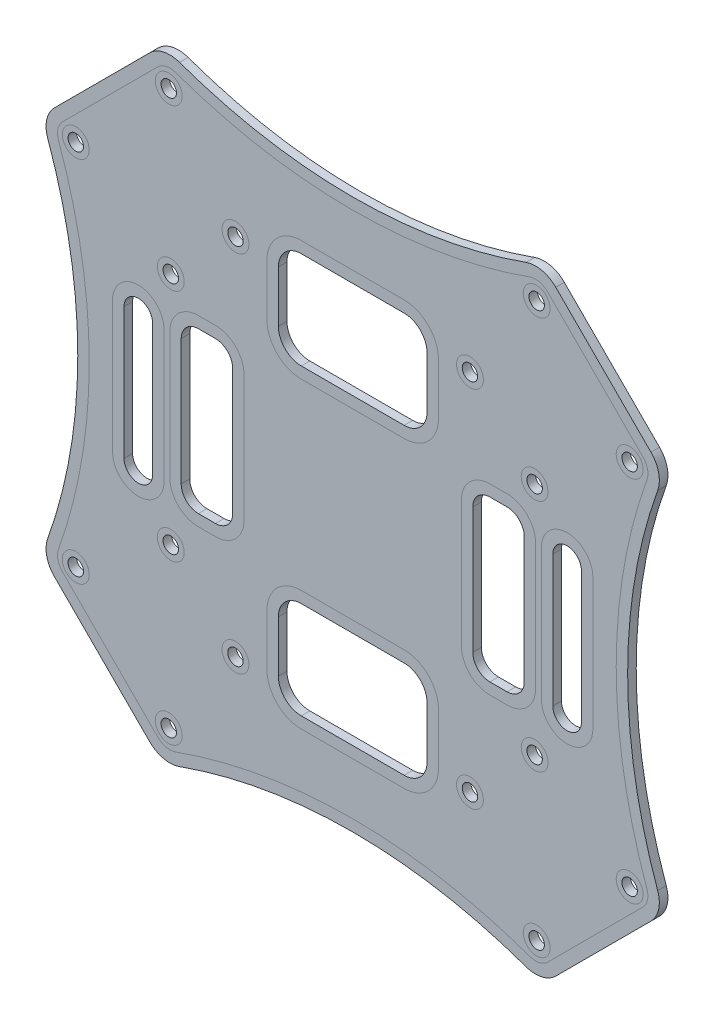
SolidWorks part; units mm, degrees
ref_plane "Ön Düzlem" through (0, 0, 0) normal (0, 0, 1) x (1, 0, 0)
ref_plane "Üst Düzlem" through (0, 0, 0) normal (0, 1, 0) x (1, 0, 0)
ref_plane "Sağ Düzlem" through (0, 0, 0) normal (1, 0, 0) x (0, 0, -1)
sketch "Çizim1" plane through (0, 0, 0) normal (0, 0, 1) x (1, 0, 0)
  line L2 (43.8406, -43.8406) -> (54.4472, -33.234)
  line L3 (43.8406, 43.8406) -> (54.4472, 33.234)
  line L4 (-9, 18) -> (9, 18)
  line L5 (-13, 22) -> (-13, 31)
  line L6 (-43.8406, 43.8406) -> (-54.4472, 33.234)
  line L7 (-43.8406, -43.8406) -> (-54.4472, -33.234)
  line L8 (-9, 35) -> (9, 35)
  line L9 (-43.8406, 43.8406) -> (-33.234, 54.4472)
  line L10 (43.8406, 43.8406) -> (33.234, 54.4472)
  line L11 (-43.8406, -43.8406) -> (-33.234, -54.4472)
  line L12 (43.8406, -43.8406) -> (33.234, -54.4472)
  line L13 (13, 22) -> (13, 31)
  line L17 (13, -22) -> (13, -31)
  line L18 (-9, -35) -> (9, -35)
  line L19 (-13, -22) -> (-13, -31)
  line L20 (-9, -18) -> (9, -18)
  line L21 (37.5, -11.5) -> (37.5, 11.5) construction
  line L22 (35, -11.5) -> (35, 11.5)
  line L23 (40, -11.5) -> (40, 11.5)
  line L24 (-37.5, -11.5) -> (-37.5, 11.5) construction
  line L25 (24, -13.3629) -> (27, -13.3629)
  line L26 (21, -10.3629) -> (21, 11.6371)
  line L27 (24, 14.6371) -> (27, 14.6371)
  line L28 (30, -10.3629) -> (30, 11.6371)
  line L31 (-35, -11.5) -> (-35, 11.5)
  line L32 (-40, -11.5) -> (-40, 11.5)
  line L35 (-30, -10.3629) -> (-30, 11.6371)
  line L36 (-24, 14.6371) -> (-27, 14.6371)
  line L37 (-21, -10.3629) -> (-21, 11.6371)
  line L38 (-24, -13.3629) -> (-27, -13.3629)
  arc A0 (54.4472, 33.234) -> (54.4472, -33.234) centre (138.0863, 0) ccw
  arc A1 (-54.4472, 33.234) -> (-54.4472, -33.234) centre (-138.0863, 0) cw
  arc A2 (-33.234, 54.4472) -> (33.234, 54.4472) centre (0, 138.0863) ccw
  arc A3 (-33.234, -54.4472) -> (33.234, -54.4472) centre (0, -138.0863) cw
  arc A4 (-13, 31) -> (-9, 35) centre (-9, 31) cw
  arc A5 (-9, 18) -> (-13, 22) centre (-9, 22) cw
  arc A6 (9, 18) -> (13, 22) centre (9, 22) ccw
  arc A7 (9, 35) -> (13, 31) centre (9, 31) cw
  arc A8 (9, -35) -> (13, -31) centre (9, -31) ccw
  arc A9 (9, -18) -> (13, -22) centre (9, -22) cw
  arc A10 (-9, -18) -> (-13, -22) centre (-9, -22) ccw
  arc A11 (-13, -31) -> (-9, -35) centre (-9, -31) ccw
  arc A12 (35, -11.5) -> (40, -11.5) centre (37.5, -11.5) ccw
  arc A13 (40, 11.5) -> (35, 11.5) centre (37.5, 11.5) ccw
  arc A14 (27, 14.6371) -> (30, 11.6371) centre (27, 11.6371) cw
  arc A15 (21, 11.6371) -> (24, 14.6371) centre (24, 11.6371) cw
  arc A16 (24, -13.3629) -> (21, -10.3629) centre (24, -10.3629) cw
  arc A17 (27, -13.3629) -> (30, -10.3629) centre (27, -10.3629) ccw
  arc A18 (-35, -11.5) -> (-40, -11.5) centre (-37.5, -11.5) cw
  arc A19 (-40, 11.5) -> (-35, 11.5) centre (-37.5, 11.5) cw
  arc A20 (-27, -13.3629) -> (-30, -10.3629) centre (-27, -10.3629) cw
  arc A21 (-24, -13.3629) -> (-21, -10.3629) centre (-24, -10.3629) ccw
  arc A22 (-21, 11.6371) -> (-24, 14.6371) centre (-24, 11.6371) ccw
  arc A23 (-27, 14.6371) -> (-30, 11.6371) centre (-27, 11.6371) ccw
  circle A24 centre (-32.1734, 48.4368) radius 1.35
  circle A25 centre (-48.4368, 32.1734) radius 1.35
  circle A26 centre (-31.8198, 20.5061) radius 1.35
  circle A27 centre (-20.5061, 31.8198) radius 1.35
  circle A28 centre (48.4368, 32.1734) radius 1.35
  circle A29 centre (32.1734, 48.4368) radius 1.35
  circle A30 centre (31.8198, 20.5061) radius 1.35
  circle A31 centre (20.5061, 31.8198) radius 1.35
  circle A32 centre (32.1734, -48.4368) radius 1.35
  circle A33 centre (48.4368, -32.1734) radius 1.35
  circle A34 centre (31.8198, -20.5061) radius 1.35
  circle A35 centre (20.5061, -31.8198) radius 1.35
  circle A36 centre (-32.1734, -48.4368) radius 1.35
  circle A37 centre (-48.4368, -32.1734) radius 1.35
  circle A38 centre (-31.8198, -20.5061) radius 1.35
  circle A39 centre (-20.5061, -31.8198) radius 1.35
  point P54 (37.5, 0)
  point P79 (-37.5, 0)
  dimension "D1" = 4
  dimension "D2" = 3
extrude "Yükseklik-Ekstrüzyon1" add sketch "Çizim1" along normal blind 1.5
fillet "Radyus1" radius 5 8 edges at (33.234, 54.4472, 0.75) (54.4472, 33.234, 0.75) (54.4472, -33.234, 0.75) (33.234, -54.4472, 0.75) (-33.234, -54.4472, 0.75) (-54.4472, -33.234, 0.75) (-54.4472, 33.234, 0.75) (-33.234, 54.4472, 0.75)
sketch "Çizim2" plane through (0, 0, 1.5) normal (0, 0, 1) x (1, 0, 0)
  line L8 (50.752, 34.1008) -> (34.1008, 50.752)
  line L9 (-34.1008, 50.752) -> (-50.752, 34.1008)
  line L10 (-50.752, -34.1008) -> (-34.1008, -50.752)
  line L11 (34.1008, -50.752) -> (50.752, -34.1008)
  line L12 (50.752, 34.1008) -> (34.1008, 50.752)
  line L13 (-34.1008, 50.752) -> (-50.752, 34.1008)
  line L14 (-50.752, -34.1008) -> (-34.1008, -50.752)
  line L15 (34.1008, -50.752) -> (50.752, -34.1008)
  line L48 (15, 22) -> (15, 31)
  line L49 (-9, 16) -> (9, 16)
  line L50 (15, 22) -> (15, 31)
  line L51 (-9, 16) -> (9, 16)
  line L57 (-15, 31) -> (-15, 22)
  line L58 (9, 37) -> (-9, 37)
  line L59 (-15, 31) -> (-15, 22)
  line L60 (9, 37) -> (-9, 37)
  line L83 (15, -31) -> (15, -22)
  line L84 (-9, -37) -> (9, -37)
  line L85 (-15, -22) -> (-15, -31)
  line L86 (9, -16) -> (-9, -16)
  line L87 (15, -31) -> (15, -22)
  line L88 (-9, -37) -> (9, -37)
  line L89 (-15, -22) -> (-15, -31)
  line L90 (9, -16) -> (-9, -16)
  line L111 (24, -15.3629) -> (27, -15.3629)
  line L112 (19, 11.6371) -> (19, -10.3629)
  line L113 (27, 16.6371) -> (24, 16.6371)
  line L114 (32, -10.3629) -> (32, 11.6371)
  line L115 (24, -15.3629) -> (27, -15.3629)
  line L116 (19, 11.6371) -> (19, -10.3629)
  line L117 (27, 16.6371) -> (24, 16.6371)
  line L118 (32, -10.3629) -> (32, 11.6371)
  line L124 (42, -11.5) -> (42, 11.5)
  line L125 (33, 11.5) -> (33, -11.5)
  line L126 (42, -11.5) -> (42, 11.5)
  line L127 (33, 11.5) -> (33, -11.5)
  line L151 (-24, 16.6371) -> (-27, 16.6371)
  line L152 (-32, 11.6371) -> (-32, -10.3629)
  line L153 (-27, -15.3629) -> (-24, -15.3629)
  line L154 (-19, -10.3629) -> (-19, 11.6371)
  line L155 (-24, 16.6371) -> (-27, 16.6371)
  line L156 (-32, 11.6371) -> (-32, -10.3629)
  line L157 (-27, -15.3629) -> (-24, -15.3629)
  line L158 (-19, -10.3629) -> (-19, 11.6371)
  line L162 (-42, 11.5) -> (-42, -11.5)
  line L163 (-33, -11.5) -> (-33, 11.5)
  line L164 (-42, 11.5) -> (-42, -11.5)
  line L165 (-33, -11.5) -> (-33, 11.5)
  arc A24 (34.1008, 50.752) -> (30.9696, 51.4556) centre (31.9795, 48.6307) ccw
  arc A25 (-30.9696, 51.4556) -> (30.9696, 51.4556) centre (0, 138.0863) ccw
  arc A26 (-30.9696, 51.4556) -> (-34.1008, 50.752) centre (-31.9795, 48.6307) ccw
  arc A27 (-50.752, 34.1008) -> (-51.4556, 30.9696) centre (-48.6307, 31.9795) ccw
  arc A28 (-51.4556, -30.9696) -> (-51.4556, 30.9696) centre (-138.0863, 0) ccw
  arc A29 (-51.4556, -30.9696) -> (-50.752, -34.1008) centre (-48.6307, -31.9795) ccw
  arc A30 (-34.1008, -50.752) -> (-30.9696, -51.4556) centre (-31.9795, -48.6307) ccw
  arc A31 (30.9696, -51.4556) -> (-30.9696, -51.4556) centre (0, -138.0863) ccw
  arc A32 (30.9696, -51.4556) -> (34.1008, -50.752) centre (31.9795, -48.6307) ccw
  arc A33 (50.752, -34.1008) -> (51.4556, -30.9696) centre (48.6307, -31.9795) ccw
  arc A34 (51.4556, 30.9696) -> (51.4556, -30.9696) centre (138.0863, 0) ccw
  arc A35 (51.4556, 30.9696) -> (50.752, 34.1008) centre (48.6307, 31.9795) ccw
  arc A36 (34.1008, 50.752) -> (30.9696, 51.4556) centre (31.9795, 48.6307) ccw
  arc A37 (-30.9696, 51.4556) -> (30.9696, 51.4556) centre (0, 138.0863) ccw
  arc A38 (-30.9696, 51.4556) -> (-34.1008, 50.752) centre (-31.9795, 48.6307) ccw
  arc A39 (-50.752, 34.1008) -> (-51.4556, 30.9696) centre (-48.6307, 31.9795) ccw
  arc A40 (-51.4556, -30.9696) -> (-51.4556, 30.9696) centre (-138.0863, 0) ccw
  arc A41 (-51.4556, -30.9696) -> (-50.752, -34.1008) centre (-48.6307, -31.9795) ccw
  arc A42 (-34.1008, -50.752) -> (-30.9696, -51.4556) centre (-31.9795, -48.6307) ccw
  arc A43 (30.9696, -51.4556) -> (-30.9696, -51.4556) centre (0, -138.0863) ccw
  arc A44 (30.9696, -51.4556) -> (34.1008, -50.752) centre (31.9795, -48.6307) ccw
  arc A45 (50.752, -34.1008) -> (51.4556, -30.9696) centre (48.6307, -31.9795) ccw
  arc A46 (51.4556, 30.9696) -> (51.4556, -30.9696) centre (138.0863, 0) ccw
  arc A47 (51.4556, 30.9696) -> (50.752, 34.1008) centre (48.6307, 31.9795) ccw
  arc A107 (15, 31) -> (9, 37) centre (9, 31) ccw
  arc A108 (9, 16) -> (15, 22) centre (9, 22) ccw
  arc A109 (-15, 22) -> (-9, 16) centre (-9, 22) ccw
  arc A110 (15, 31) -> (9, 37) centre (9, 31) ccw
  arc A111 (9, 16) -> (15, 22) centre (9, 22) ccw
  arc A112 (-15, 22) -> (-9, 16) centre (-9, 22) ccw
  arc A113 (-9, 37) -> (-15, 31) centre (-9, 31) ccw
  arc A114 (-9, 37) -> (-15, 31) centre (-9, 31) ccw
  circle A129 centre (-32.1734, 48.4368) radius 2.35
  circle A130 centre (-32.1734, 48.4368) radius 2.35
  circle A132 centre (-20.5061, 31.8198) radius 2.35
  circle A133 centre (-20.5061, 31.8198) radius 2.35
  circle A135 centre (-31.8198, 20.5061) radius 2.35
  circle A136 centre (-31.8198, 20.5061) radius 2.35
  circle A138 centre (-48.4368, 32.1734) radius 2.35
  circle A139 centre (-48.4368, 32.1734) radius 2.35
  circle A141 centre (32.1734, 48.4368) radius 2.35
  circle A142 centre (32.1734, 48.4368) radius 2.35
  circle A144 centre (20.5061, 31.8198) radius 2.35
  circle A145 centre (20.5061, 31.8198) radius 2.35
  circle A147 centre (31.8198, 20.5061) radius 2.35
  circle A148 centre (31.8198, 20.5061) radius 2.35
  circle A150 centre (48.4368, 32.1734) radius 2.35
  circle A151 centre (48.4368, 32.1734) radius 2.35
  circle A153 centre (31.8198, -20.5061) radius 2.35
  circle A154 centre (31.8198, -20.5061) radius 2.35
  circle A156 centre (48.4368, -32.1734) radius 2.35
  circle A157 centre (48.4368, -32.1734) radius 2.35
  circle A159 centre (20.5061, -31.8198) radius 2.35
  circle A160 centre (20.5061, -31.8198) radius 2.35
  circle A162 centre (32.1734, -48.4368) radius 2.35
  circle A163 centre (32.1734, -48.4368) radius 2.35
  circle A165 centre (-20.5061, -31.8198) radius 2.35
  circle A166 centre (-20.5061, -31.8198) radius 2.35
  circle A168 centre (-31.8198, -20.5061) radius 2.35
  circle A169 centre (-31.8198, -20.5061) radius 2.35
  circle A171 centre (-48.4368, -32.1734) radius 2.35
  circle A172 centre (-48.4368, -32.1734) radius 2.35
  circle A174 centre (-32.1734, -48.4368) radius 2.35
  circle A175 centre (-32.1734, -48.4368) radius 2.35
  arc A195 (15, -22) -> (9, -16) centre (9, -22) ccw
  arc A196 (9, -37) -> (15, -31) centre (9, -31) ccw
  arc A197 (-15, -31) -> (-9, -37) centre (-9, -31) ccw
  arc A198 (-9, -16) -> (-15, -22) centre (-9, -22) ccw
  arc A199 (15, -22) -> (9, -16) centre (9, -22) ccw
  arc A200 (9, -37) -> (15, -31) centre (9, -31) ccw
  arc A201 (-15, -31) -> (-9, -37) centre (-9, -31) ccw
  arc A202 (-9, -16) -> (-15, -22) centre (-9, -22) ccw
  arc A219 (27, -15.3629) -> (32, -10.3629) centre (27, -10.3629) ccw
  arc A220 (19, -10.3629) -> (24, -15.3629) centre (24, -10.3629) ccw
  arc A221 (24, 16.6371) -> (19, 11.6371) centre (24, 11.6371) ccw
  arc A222 (32, 11.6371) -> (27, 16.6371) centre (27, 11.6371) ccw
  arc A223 (27, -15.3629) -> (32, -10.3629) centre (27, -10.3629) ccw
  arc A224 (19, -10.3629) -> (24, -15.3629) centre (24, -10.3629) ccw
  arc A225 (24, 16.6371) -> (19, 11.6371) centre (24, 11.6371) ccw
  arc A226 (32, 11.6371) -> (27, 16.6371) centre (27, 11.6371) ccw
  arc A229 (33, -11.5) -> (42, -11.5) centre (37.5, -11.5) ccw
  arc A230 (42, 11.5) -> (33, 11.5) centre (37.5, 11.5) ccw
  arc A231 (33, -11.5) -> (42, -11.5) centre (37.5, -11.5) ccw
  arc A232 (42, 11.5) -> (33, 11.5) centre (37.5, 11.5) ccw
  arc A251 (-19, 11.6371) -> (-24, 16.6371) centre (-24, 11.6371) ccw
  arc A252 (-27, 16.6371) -> (-32, 11.6371) centre (-27, 11.6371) ccw
  arc A253 (-32, -10.3629) -> (-27, -15.3629) centre (-27, -10.3629) ccw
  arc A254 (-24, -15.3629) -> (-19, -10.3629) centre (-24, -10.3629) ccw
  arc A255 (-19, 11.6371) -> (-24, 16.6371) centre (-24, 11.6371) ccw
  arc A256 (-27, 16.6371) -> (-32, 11.6371) centre (-27, 11.6371) ccw
  arc A257 (-32, -10.3629) -> (-27, -15.3629) centre (-27, -10.3629) ccw
  arc A258 (-24, -15.3629) -> (-19, -10.3629) centre (-24, -10.3629) ccw
  arc A262 (-42, -11.5) -> (-33, -11.5) centre (-37.5, -11.5) ccw
  arc A263 (-33, 11.5) -> (-42, 11.5) centre (-37.5, 11.5) ccw
  arc A264 (-42, -11.5) -> (-33, -11.5) centre (-37.5, -11.5) ccw
  arc A265 (-33, 11.5) -> (-42, 11.5) centre (-37.5, 11.5) ccw
  dimension "D1" = 2
  dimension "D2" = 2
  dimension "D3" = 2
  dimension "D4" = 1
  dimension "D5" = 1
  dimension "D6" = 1
  dimension "D7" = 1
  dimension "D8" = 1
  dimension "D9" = 1
  dimension "D10" = 1
  dimension "D11" = 1
  dimension "D12" = 1
  dimension "D13" = 1
  dimension "D14" = 1
  dimension "D15" = 1
  dimension "D16" = 1
  dimension "D17" = 1
  dimension "D18" = 1
  dimension "D19" = 1
  dimension "D20" = 2
  dimension "D21" = 2
  dimension "D22" = 2
  dimension "D23" = 2
  dimension "D24" = 2
split line "Ayrım Çizgisi1"
sketch "Çizim3" plane through (0, 0, 0) normal (0, 0, -1) x (-1, 0, 0)
  line L8 (-34.1008, 50.752) -> (-50.752, 34.1008)
  line L9 (-50.752, -34.1008) -> (-34.1008, -50.752)
  line L10 (34.1008, -50.752) -> (50.752, -34.1008)
  line L11 (50.752, 34.1008) -> (34.1008, 50.752)
  line L12 (-34.1008, 50.752) -> (-50.752, 34.1008)
  line L13 (-50.752, -34.1008) -> (-34.1008, -50.752)
  line L14 (34.1008, -50.752) -> (50.752, -34.1008)
  line L15 (50.752, 34.1008) -> (34.1008, 50.752)
  line L36 (15, 22) -> (15, 31)
  line L37 (-9, 16) -> (9, 16)
  line L38 (-15, 31) -> (-15, 22)
  line L39 (9, 37) -> (-9, 37)
  line L40 (15, 22) -> (15, 31)
  line L41 (-9, 16) -> (9, 16)
  line L42 (-15, 31) -> (-15, 22)
  line L43 (9, 37) -> (-9, 37)
  line L76 (32, -10.3629) -> (32, 11.6371)
  line L77 (24, -15.3629) -> (27, -15.3629)
  line L78 (19, 11.6371) -> (19, -10.3629)
  line L79 (27, 16.6371) -> (24, 16.6371)
  line L80 (32, -10.3629) -> (32, 11.6371)
  line L81 (24, -15.3629) -> (27, -15.3629)
  line L82 (19, 11.6371) -> (19, -10.3629)
  line L83 (27, 16.6371) -> (24, 16.6371)
  line L88 (33, -11.5) -> (33, 11.5)
  line L89 (33, -11.5) -> (33, 11.5)
  line L94 (42, -11.5) -> (42, 11.5)
  line L95 (42, -11.5) -> (42, 11.5)
  line L119 (-27, -15.3629) -> (-24, -15.3629)
  line L120 (-32, 11.6371) -> (-32, -10.3629)
  line L121 (-24, 16.6371) -> (-27, 16.6371)
  line L122 (-19, -10.3629) -> (-19, 11.6371)
  line L123 (-27, -15.3629) -> (-24, -15.3629)
  line L124 (-32, 11.6371) -> (-32, -10.3629)
  line L125 (-24, 16.6371) -> (-27, 16.6371)
  line L126 (-19, -10.3629) -> (-19, 11.6371)
  line L130 (-42, 11.5) -> (-42, -11.5)
  line L131 (-33, -11.5) -> (-33, 11.5)
  line L132 (-42, 11.5) -> (-42, -11.5)
  line L133 (-33, -11.5) -> (-33, 11.5)
  line L156 (15, -31) -> (15, -22)
  line L157 (-9, -37) -> (9, -37)
  line L158 (-15, -22) -> (-15, -31)
  line L159 (9, -16) -> (-9, -16)
  line L160 (15, -31) -> (15, -22)
  line L161 (-9, -37) -> (9, -37)
  line L162 (-15, -22) -> (-15, -31)
  line L163 (9, -16) -> (-9, -16)
  arc A24 (-30.9696, 51.4556) -> (30.9696, 51.4556) centre (0, 138.0863) ccw
  arc A25 (-30.9696, 51.4556) -> (-34.1008, 50.752) centre (-31.9795, 48.6307) ccw
  arc A26 (-50.752, 34.1008) -> (-51.4556, 30.9696) centre (-48.6307, 31.9795) ccw
  arc A27 (-51.4556, -30.9696) -> (-51.4556, 30.9696) centre (-138.0863, 0) ccw
  arc A28 (-51.4556, -30.9696) -> (-50.752, -34.1008) centre (-48.6307, -31.9795) ccw
  arc A29 (-34.1008, -50.752) -> (-30.9696, -51.4556) centre (-31.9795, -48.6307) ccw
  arc A30 (30.9696, -51.4556) -> (-30.9696, -51.4556) centre (0, -138.0863) ccw
  arc A31 (30.9696, -51.4556) -> (34.1008, -50.752) centre (31.9795, -48.6307) ccw
  arc A32 (50.752, -34.1008) -> (51.4556, -30.9696) centre (48.6307, -31.9795) ccw
  arc A33 (51.4556, 30.9696) -> (51.4556, -30.9696) centre (138.0863, 0) ccw
  arc A34 (51.4556, 30.9696) -> (50.752, 34.1008) centre (48.6307, 31.9795) ccw
  arc A35 (34.1008, 50.752) -> (30.9696, 51.4556) centre (31.9795, 48.6307) ccw
  arc A36 (-30.9696, 51.4556) -> (30.9696, 51.4556) centre (0, 138.0863) ccw
  arc A37 (-30.9696, 51.4556) -> (-34.1008, 50.752) centre (-31.9795, 48.6307) ccw
  arc A38 (-50.752, 34.1008) -> (-51.4556, 30.9696) centre (-48.6307, 31.9795) ccw
  arc A39 (-51.4556, -30.9696) -> (-51.4556, 30.9696) centre (-138.0863, 0) ccw
  arc A40 (-51.4556, -30.9696) -> (-50.752, -34.1008) centre (-48.6307, -31.9795) ccw
  arc A41 (-34.1008, -50.752) -> (-30.9696, -51.4556) centre (-31.9795, -48.6307) ccw
  arc A42 (30.9696, -51.4556) -> (-30.9696, -51.4556) centre (0, -138.0863) ccw
  arc A43 (30.9696, -51.4556) -> (34.1008, -50.752) centre (31.9795, -48.6307) ccw
  arc A44 (50.752, -34.1008) -> (51.4556, -30.9696) centre (48.6307, -31.9795) ccw
  arc A45 (51.4556, 30.9696) -> (51.4556, -30.9696) centre (138.0863, 0) ccw
  arc A46 (51.4556, 30.9696) -> (50.752, 34.1008) centre (48.6307, 31.9795) ccw
  arc A47 (34.1008, 50.752) -> (30.9696, 51.4556) centre (31.9795, 48.6307) ccw
  arc A56 (15, 31) -> (9, 37) centre (9, 31) ccw
  arc A57 (9, 16) -> (15, 22) centre (9, 22) ccw
  arc A58 (-15, 22) -> (-9, 16) centre (-9, 22) ccw
  arc A59 (-9, 37) -> (-15, 31) centre (-9, 31) ccw
  arc A60 (15, 31) -> (9, 37) centre (9, 31) ccw
  arc A61 (9, 16) -> (15, 22) centre (9, 22) ccw
  arc A62 (-15, 22) -> (-9, 16) centre (-9, 22) ccw
  arc A63 (-9, 37) -> (-15, 31) centre (-9, 31) ccw
  arc A96 (27, -15.3629) -> (32, -10.3629) centre (27, -10.3629) ccw
  arc A97 (19, -10.3629) -> (24, -15.3629) centre (24, -10.3629) ccw
  arc A98 (24, 16.6371) -> (19, 11.6371) centre (24, 11.6371) ccw
  arc A99 (32, 11.6371) -> (27, 16.6371) centre (27, 11.6371) ccw
  arc A100 (27, -15.3629) -> (32, -10.3629) centre (27, -10.3629) ccw
  arc A101 (19, -10.3629) -> (24, -15.3629) centre (24, -10.3629) ccw
  arc A102 (24, 16.6371) -> (19, 11.6371) centre (24, 11.6371) ccw
  arc A103 (32, 11.6371) -> (27, 16.6371) centre (27, 11.6371) ccw
  arc A105 (42, 11.5) -> (33, 11.5) centre (37.5, 11.5) ccw
  arc A106 (33, -11.5) -> (42, -11.5) centre (37.5, -11.5) ccw
  arc A107 (42, 11.5) -> (33, 11.5) centre (37.5, 11.5) ccw
  arc A108 (33, -11.5) -> (42, -11.5) centre (37.5, -11.5) ccw
  arc A127 (-24, -15.3629) -> (-19, -10.3629) centre (-24, -10.3629) ccw
  arc A128 (-32, -10.3629) -> (-27, -15.3629) centre (-27, -10.3629) ccw
  arc A129 (-27, 16.6371) -> (-32, 11.6371) centre (-27, 11.6371) ccw
  arc A130 (-19, 11.6371) -> (-24, 16.6371) centre (-24, 11.6371) ccw
  arc A131 (-24, -15.3629) -> (-19, -10.3629) centre (-24, -10.3629) ccw
  arc A132 (-32, -10.3629) -> (-27, -15.3629) centre (-27, -10.3629) ccw
  arc A133 (-27, 16.6371) -> (-32, 11.6371) centre (-27, 11.6371) ccw
  arc A134 (-19, 11.6371) -> (-24, 16.6371) centre (-24, 11.6371) ccw
  arc A138 (-42, -11.5) -> (-33, -11.5) centre (-37.5, -11.5) ccw
  arc A139 (-33, 11.5) -> (-42, 11.5) centre (-37.5, 11.5) ccw
  arc A140 (-42, -11.5) -> (-33, -11.5) centre (-37.5, -11.5) ccw
  arc A141 (-33, 11.5) -> (-42, 11.5) centre (-37.5, 11.5) ccw
  circle A158 centre (-48.4368, 32.1734) radius 2.35
  circle A159 centre (-48.4368, 32.1734) radius 2.35
  arc A160 (15, -22) -> (9, -16) centre (9, -22) ccw
  arc A161 (9, -37) -> (15, -31) centre (9, -31) ccw
  arc A162 (-15, -31) -> (-9, -37) centre (-9, -31) ccw
  arc A163 (-9, -16) -> (-15, -22) centre (-9, -22) ccw
  arc A164 (15, -22) -> (9, -16) centre (9, -22) ccw
  arc A165 (9, -37) -> (15, -31) centre (9, -31) ccw
  arc A166 (-15, -31) -> (-9, -37) centre (-9, -31) ccw
  arc A167 (-9, -16) -> (-15, -22) centre (-9, -22) ccw
  circle A169 centre (-32.1734, 48.4368) radius 2.35
  circle A170 centre (-32.1734, 48.4368) radius 2.35
  circle A172 centre (-20.5061, 31.8198) radius 2.35
  circle A173 centre (-20.5061, 31.8198) radius 2.35
  circle A175 centre (-31.8198, 20.5061) radius 2.35
  circle A176 centre (-31.8198, 20.5061) radius 2.35
  circle A178 centre (20.5061, 31.8198) radius 2.35
  circle A179 centre (20.5061, 31.8198) radius 2.35
  circle A181 centre (32.1734, 48.4368) radius 2.35
  circle A182 centre (32.1734, 48.4368) radius 2.35
  circle A184 centre (48.4368, 32.1734) radius 2.35
  circle A185 centre (48.4368, 32.1734) radius 2.35
  circle A187 centre (31.8198, 20.5061) radius 2.35
  circle A188 centre (31.8198, 20.5061) radius 2.35
  circle A190 centre (31.8198, -20.5061) radius 2.35
  circle A191 centre (31.8198, -20.5061) radius 2.35
  circle A193 centre (48.4368, -32.1734) radius 2.35
  circle A194 centre (48.4368, -32.1734) radius 2.35
  circle A196 centre (20.5061, -31.8198) radius 2.35
  circle A197 centre (20.5061, -31.8198) radius 2.35
  circle A199 centre (32.1734, -48.4368) radius 2.35
  circle A200 centre (32.1734, -48.4368) radius 2.35
  circle A202 centre (-32.1734, -48.4368) radius 2.35
  circle A203 centre (-32.1734, -48.4368) radius 2.35
  circle A205 centre (-20.5061, -31.8198) radius 2.35
  circle A206 centre (-20.5061, -31.8198) radius 2.35
  circle A208 centre (-31.8198, -20.5061) radius 2.35
  circle A209 centre (-31.8198, -20.5061) radius 2.35
  circle A211 centre (-48.4368, -32.1734) radius 2.35
  circle A212 centre (-48.4368, -32.1734) radius 2.35
  dimension "D1" = 2
  dimension "D2" = 2
  dimension "D3" = 2
  dimension "D4" = 2
  dimension "D5" = 2
  dimension "D6" = 2
  dimension "D7" = 2
  dimension "D8" = 2
  dimension "D9" = 1
  dimension "D10" = 1
  dimension "D11" = 1
  dimension "D12" = 1
  dimension "D13" = 1
  dimension "D14" = 1
  dimension "D15" = 1
  dimension "D16" = 1
  dimension "D17" = 1
  dimension "D18" = 1
  dimension "D19" = 1
  dimension "D20" = 1
  dimension "D21" = 1
  dimension "D22" = 1
  dimension "D23" = 1
  dimension "D24" = 1
split line "Ayrım Çizgisi2"
